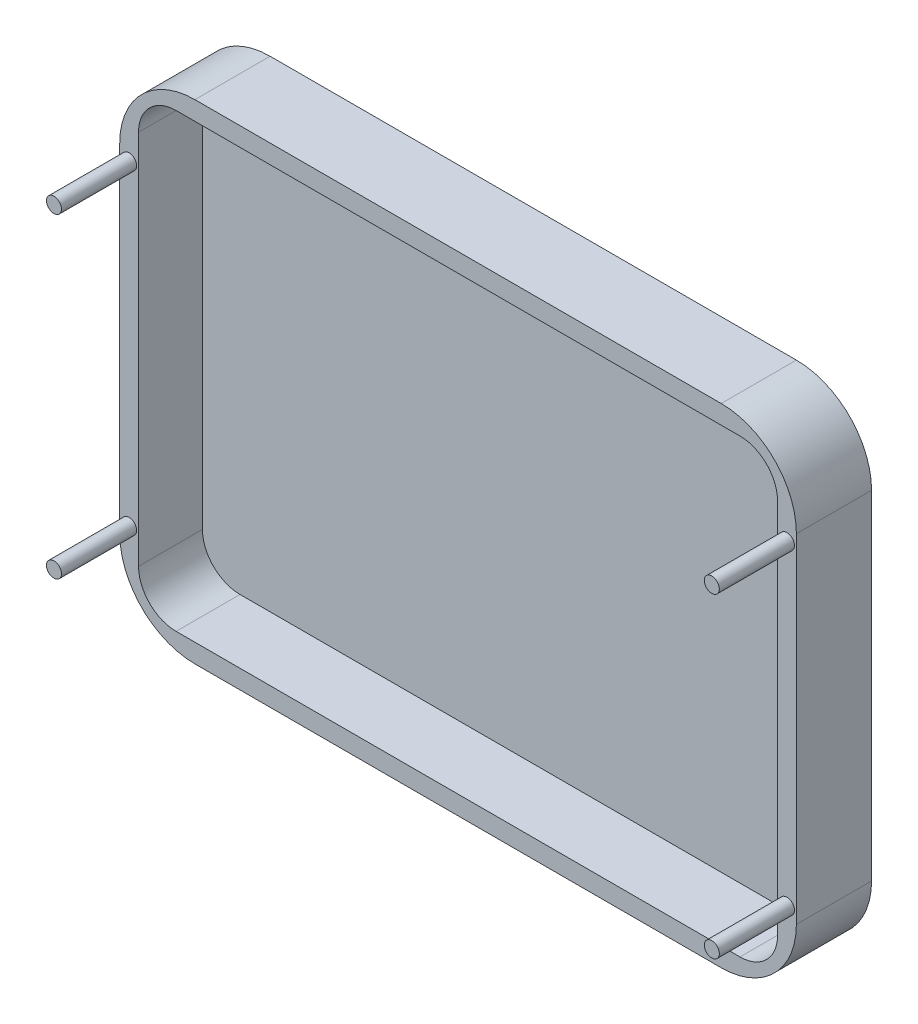
SolidWorks part; units mm, degrees
ref_plane "Front Plane" through (0, 0, 0) normal (0, 0, 1) x (1, 0, 0)
ref_plane "Top Plane" through (0, 0, 0) normal (0, 1, 0) x (1, 0, 0)
ref_plane "Right Plane" through (0, 0, 0) normal (1, 0, 0) x (0, 0, -1)
sketch "Sketch1" plane through (0, 0, 0) normal (0, 0, 1) x (1, 0, 0)
  line L1 (-64.9556, 61.2444) -> (75.0444, 61.2444)
  line L2 (-84.9556, 41.2444) -> (-84.9556, -48.7556)
  line L3 (-64.9556, -68.7556) -> (75.0444, -68.7556)
  line L4 (95.0444, 41.2444) -> (95.0444, -48.7556)
  arc A0 (75.0444, 61.2444) -> (95.0444, 41.2444) centre (75.0444, 41.2444) cw
  arc A1 (75.0444, -68.7556) -> (95.0444, -48.7556) centre (75.0444, -48.7556) ccw
  arc A2 (-84.9556, -48.7556) -> (-64.9556, -68.7556) centre (-64.9556, -48.7556) ccw
  arc A3 (-64.9556, 61.2444) -> (-84.9556, 41.2444) centre (-64.9556, 41.2444) ccw
  point P6 (95.0444, 61.2444)
  point P9 (95.0444, -68.7556)
  point P12 (-84.9556, -68.7556)
  dimension "D3" = 20
  dimension "D1" = 130
  dimension "D2" = 180
extrude "Boss-Extrude1" add sketch "Sketch1" along normal blind 20
sketch "Sketch2" plane through (0, 0, 20) normal (0, 0, 1) x (1, 0, 0)
  line L0 (-64.9556, -68.7556) -> (75.0444, -68.7556) construction
  line L1 (-69.9556, 56.2444) -> (80.0444, 56.2444)
  line L2 (-79.9556, 46.2444) -> (-79.9556, -53.7556)
  line L3 (-69.9556, -63.7556) -> (80.0444, -63.7556)
  line L4 (90.0444, 46.2444) -> (90.0444, -53.7556)
  line L5 (-84.9556, 41.2444) -> (-84.9556, -48.7556) construction
  arc A0 (80.0444, 56.2444) -> (90.0444, 46.2444) centre (80.0444, 46.2444) cw
  arc A1 (80.0444, -63.7556) -> (90.0444, -53.7556) centre (80.0444, -53.7556) ccw
  arc A2 (-79.9556, -53.7556) -> (-69.9556, -63.7556) centre (-69.9556, -53.7556) ccw
  arc A3 (-69.9556, 56.2444) -> (-79.9556, 46.2444) centre (-69.9556, 46.2444) ccw
  dimension "D1" = 10
  dimension "D2" = 100
  dimension "D3" = 150
  dimension "D4" = 5
  dimension "D5" = 5
extrude "Cut-Extrude1" cut sketch "Sketch2" against normal blind 17
sketch "Sketch3" plane through (0, 0, 20) normal (0, 0, 1) x (1, 0, 0)
  line L0 (75.0444, 61.2444) -> (-64.9556, 61.2444) construction
  line L1 (-64.9556, -68.7556) -> (75.0444, -68.7556) construction
  line L2 (95.0444, -48.7556) -> (95.0444, 41.2444) construction
  line L3 (-79.9556, 46.2444) -> (-79.9556, -53.7556) construction
  circle A0 centre (-82.4556, 38.2444) radius 2
  circle A1 centre (-82.4556, -45.7556) radius 2
  circle A2 centre (92.5444, -45.7556) radius 2
  circle A3 centre (92.5444, 38.2444) radius 2
  dimension "D1" = 4
  dimension "D2" = 4
  dimension "D3" = 4
  dimension "D4" = 4
  dimension "D5" = 23
  dimension "D6" = 23
  dimension "D7" = 23
  dimension "D8" = 23
  dimension "D9" = 2.5
  dimension "D10" = 2.5
  dimension "D11" = 2.5
  dimension "D12" = 2.5
extrude "Boss-Extrude3" add sketch "Sketch3" along normal blind 20
